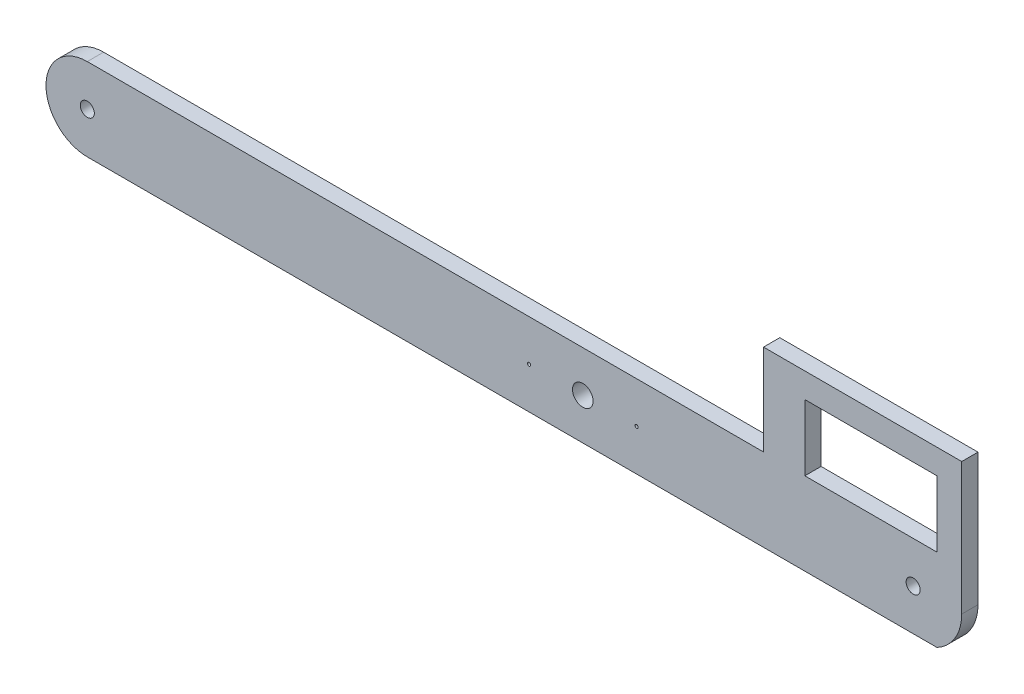
SolidWorks part; units mm, degrees
ref_plane "Front Plane" through (0, 0, 0) normal (0, 0, 1) x (1, 0, 0)
ref_plane "Top Plane" through (0, 0, 0) normal (0, 1, 0) x (1, 0, 0)
ref_plane "Right Plane" through (0, 0, 0) normal (1, 0, 0) x (0, 0, -1)
sketch "Sketch1" plane through (0, 0, 0) normal (0, 0, 1) x (1, 0, 0)
  line L0 (-152.4, 12.7) -> (-152.4, -12.7) construction
  line L1 (-173.5503, 12.7) -> (129.1788, 12.7)
  line L2 (-173.5503, 12.7) -> (-173.5503, -12.7)
  line L3 (-173.5503, -12.7) -> (129.1788, -12.7)
  line L4 (129.1788, 12.7) -> (129.1788, -12.7)
  line L6 (-152.4, 0) -> (0, 0) construction
  line L7 (0, 0) -> (101.6, 0) construction
  line L12 (-139.7, -8.89) -> (-12.7, 8.89) construction
  line L13 (-139.7, 8.89) -> (-12.7, -8.89) construction
  line L18 (12.7, 8.89) -> (88.9, -8.89) construction
  line L19 (12.7, -8.89) -> (88.9, 8.89) construction
  line L20 (116.543, 0) -> (116.543, 29.21)
  line L21 (102.87, 40.64) -> (77.47, 40.64)
  line L22 (55.583, 21.59) -> (55.583, 12.7)
  line L23 (55.583, 12.7) -> (68.283, 12.7)
  line L24 (68.283, 12.7) -> (108.923, 12.7)
  line L25 (68.283, 12.7) -> (68.283, 33.02)
  line L26 (68.283, 33.02) -> (108.923, 33.02)
  line L27 (108.923, 12.7) -> (108.923, 33.02)
  line L28 (108.923, 12.7) -> (116.543, 12.7)
  line L30 (116.543, 12.7) -> (55.583, 12.7)
  line L31 (116.543, 12.7) -> (116.543, 40.64)
  line L32 (116.543, 40.64) -> (55.583, 40.64)
  line L33 (55.583, 12.7) -> (55.583, 40.64)
  circle A0 centre (0, 0) radius 3.175
  circle A1 centre (101.6, 0) radius 6.35
  circle A2 centre (-152.4, 0) radius 6.35
  arc A3 (-152.4, -12.7) -> (-152.4, 12.7) centre (-152.4, 0) cw
  arc A4 (108.923, -12.7) -> (108.923, 12.7) centre (102.1497, 0) ccw
  point P14 (-152.4, 0)
  point P17 (0, 0)
  point P18 (101.6, 0)
  point P20 (-76.2, 0)
  point P21 (50.8, 0)
  point P40 (109.3456, 14.5449)
  dimension "D3" = 12.7
  dimension "D4" = 6.35
  dimension "D5" = 12.7
  dimension "D6" = 12.7
  dimension "D1" = 152.4
  dimension "D2" = 101.6
  dimension "D7" = 12.7
  dimension "D16" = 20.32
  dimension "D17" = 7.62
  dimension "D18" = 7.62
  dimension "D19" = 12.7
  dimension "D20" = 40.64
extrude "Boss-Extrude1" add sketch "Sketch1" along normal blind 5.0038
sketch "Sketch2" plane through (0, 0, 5.0038) normal (0, 0, 1) x (1, 0, 0)
  circle A0 centre (-152.4, 0) radius 10.4258
  circle A1 centre (-152.4, 0) radius 2.159
  circle A2 centre (101.6, 0) radius 8.1429
  circle A3 centre (101.6, 0) radius 2.159
  dimension "D1" = 4.318
  dimension "D2" = 4.318
extrude "Boss-Extrude2" add sketch "Sketch2" against normal blind 5.0038
sketch "Sketch3" plane through (0, 0, 0) normal (0, 0, -1) x (-1, 0, 0)
  circle A0 centre (16.5354, 0) radius 0.5
  circle A1 centre (-16.5354, 0) radius 0.5
  dimension "D1" = 1
  dimension "D2" = 1
  dimension "D3" = 16.5354
  dimension "D4" = 16.5354
extrude "Cut-Extrude1" cut sketch "Sketch3" against normal blind 19.304
